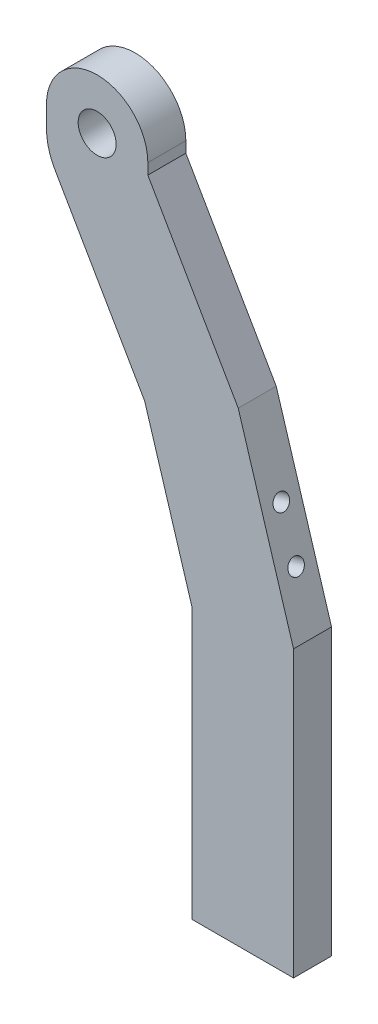
SolidWorks part; units mm, degrees
ref_plane "前视基准面" through (0, 0, 0) normal (0, 0, 1) x (1, 0, 0)
ref_plane "上视基准面" through (0, 0, 0) normal (0, 1, 0) x (1, 0, 0)
ref_plane "右视基准面" through (0, 0, 0) normal (1, 0, 0) x (0, 0, -1)
sketch "草图1" plane through (0, 0, 0) normal (0, 0, 1) x (1, 0, 0)
  line L0 (19.1673, 7.9395) -> (-3.8327, 47.7766)
  line L1 (-3.8327, 47.7766) -> (-3.8327, 49.4894)
  line L2 (-19.8327, 49.4894) -> (-19.8327, 43.4894)
  line L3 (-19.8327, 43.4894) -> (3.1673, 3.6523)
  line L4 (3.1673, 3.6523) -> (3.1673, -56.4913)
  line L5 (3.1673, -56.4913) -> (19.1673, -56.4913)
  line L6 (19.1673, -56.4913) -> (19.1673, 7.9395)
  line L7 (-98.5403, 0) -> (83.3843, 0) construction
  line L8 (0, 94.82) -> (0, -96.7069) construction
  arc A0 (-3.8327, 49.4894) -> (-19.8327, 49.4894) centre (-11.8327, 49.4894) ccw
  circle A1 centre (-11.8327, 49.4894) radius 3
  point P16 (11.1673, -56.4913)
  dimension "D2" = 6
  dimension "D3" = 49.4894
  dimension "D4" = 11.8327
  dimension "D8" = 8
  dimension "D1" = 56.4913
  dimension "D5" = 6.3346
  dimension "D6" = 19.1673
  dimension "D7" = 16
  dimension "D9" = 30
extrude "凸台-拉伸1" add sketch "草图1" along normal blind 6
sketch "草图2" plane through (0, -56.4913, 0) normal (0, -1, 0) x (1, 0, 0)
  line L0 (3.1673, -20) -> (19.1673, -20)
  line L1 (19.1673, -20) -> (19.1673, 6)
  line L2 (19.1673, 6) -> (3.1673, 6)
  line L3 (3.1673, 6) -> (3.1673, -20)
  circle A0 centre (7.1673, -8) radius 1.6
  circle A1 centre (15.1673, -15) radius 1.6
extrude "凸台-拉伸2" add sketch "草图2" against normal blind 6
fillet "圆角2" radius 10 1 edges at (-19.8327, 43.4894, 3)
fillet "圆角3" radius 2 2 edges at (3.1673, -53.4913, -20) (19.1673, -53.4913, -20)
sketch "草图3" plane through (19.1673, 0, 0) normal (1, 0, 0) x (0, 0, -1)
  line L0 (18, -50.4913) -> (0, -50.4913) construction
  line L1 (-11.8195, -50.4913) -> (27.952, -50.4913)
  line L2 (-11.8195, -50.4913) -> (-11.8195, -66.0603)
  line L3 (-11.8195, -66.0603) -> (27.952, -66.0603)
  line L4 (27.952, -50.4913) -> (27.952, -66.0603)
extrude "切除-拉伸1" cut sketch "草图3" against normal up to surface (16 mm away) up to face at (3.1673, -34.4435, -4)
hole_wizard "M3 螺纹孔1" positions "草图4" profile "草图5" tap size "M3" standard "GB"
sketch "草图4" plane through (0, -50.4913, 0) normal (0, -1, 0) x (-1, 0, 0)
  line L1 (-19.1673, -6) -> (-3.1673, -6) construction
  line L2 (-3.1673, -6) -> (-3.1673, 0) construction
  line L3 (-19.1673, 0) -> (-19.1673, -6) construction
  point P0 (-7.6673, -3)
  point P2 (-14.6673, -3)
  dimension "D1" = 3
  dimension "D2" = 4.5
  dimension "D3" = 3
  dimension "D4" = 4.5
sketch "草图5" plane through (7.6673, -50.4913, 3) normal (1, 0, 0) x (0, 0, -1)
  line L0 (0, 0) -> (0, 8.2511)
  line L1 (0, 8.2511) -> (1.25, 7.5)
  line L2 (1.25, 7.5) -> (1.25, 0)
  line L5 (1.25, 0) -> (0, 0)
  line L10 (0, 8.2511) -> (-1.25, 7.5) construction
  line L11 (0, -6.35) -> (0, 107.95) construction
  dimension "螺纹孔钻头直径" = 2.5
  dimension "螺纹孔钻头深度" = 7.5
  dimension "导头角度" = 118
cosmetic thread "孔螺蚊线1" parameters "D1"=6, "D2"=3
cosmetic thread "孔螺蚊线2" parameters "D1"=6, "D2"=3
sketch "草图9" plane through (0, 0, 6) normal (0, 0, 1) x (1, 0, 0)
  line L0 (19.1673, 7.9395) -> (-3.8327, 47.7766) construction
  line L1 (10.4392, 23.0569) -> (29.9258, 19.3386)
  line L2 (10.4392, 23.0569) -> (19.1673, -5.4913)
  line L3 (19.1673, -50.4913) -> (19.1673, 7.9395) construction
  line L4 (29.9258, 19.3386) -> (19.1673, -5.4913)
  line L6 (19.1673, -50.4913) -> (3.1673, -50.4913) construction
  dimension "D1" = 45
  dimension "D2" = 163
extrude "切除-拉伸2" cut sketch "草图9" against normal through all
sketch "草图12" plane through (0, 0, 6) normal (0, 0, 1) x (1, 0, 0)
  line L0 (-4.3287, 16.6357) -> (3.1673, -7.8825)
  line L1 (-18.493, 41.1689) -> (3.1673, 3.6523) construction
  line L2 (3.1673, 3.6523) -> (3.1673, -50.4913) construction
  line L3 (3.1673, -7.8825) -> (3.1673, 3.6523)
  line L4 (3.1673, 3.6523) -> (-4.3287, 16.6357)
  line L5 (10.4392, 23.0569) -> (19.1673, -5.4913) construction
  dimension "D1" = 16
extrude "凸台-拉伸3" add sketch "草图12" against normal up to surface (6 mm away) up to face at (-8.8327, 49.4894, 0)
hole_wizard "M3 螺纹孔3" positions "3D草图2" profile "草图13" tap size "M3" standard "GB"
sketch3d "3D草图2"
  line L0 (14.2401, 10.625, 3) -> (16.579, 2.9745, 3) construction
  line L2 (10.4392, 23.0569, 6) -> (19.1673, -5.4913, 6) construction
  line L4 (10.4392, 23.0569, 0) -> (10.4392, 23.0569, 6) construction
  point P0 (14.2401, 10.625, 3)
  point P2 (16.579, 2.9745, 3)
  dimension "D1" = 3
  dimension "D2" = 8
  dimension "D3" = 13
sketch "草图13" plane through (14.2401, 10.625, 3) normal (0, 0, 1) x (-0.2924, 0.9563, 0)
  line L0 (0, 0) -> (0, 8.2511)
  line L1 (0, 8.2511) -> (1.25, 7.5)
  line L2 (1.25, 7.5) -> (1.25, 0)
  line L5 (1.25, 0) -> (0, 0)
  line L10 (0, 8.2511) -> (-1.25, 7.5) construction
  line L11 (0, -6.35) -> (0, 107.95) construction
  dimension "螺纹孔钻头直径" = 2.5
  dimension "螺纹孔钻头深度" = 7.5
  dimension "导头角度" = 118
cosmetic thread "孔螺蚊线8" parameters "D1"=6, "D2"=3
cosmetic thread "孔螺蚊线9" parameters "D1"=6, "D2"=3
